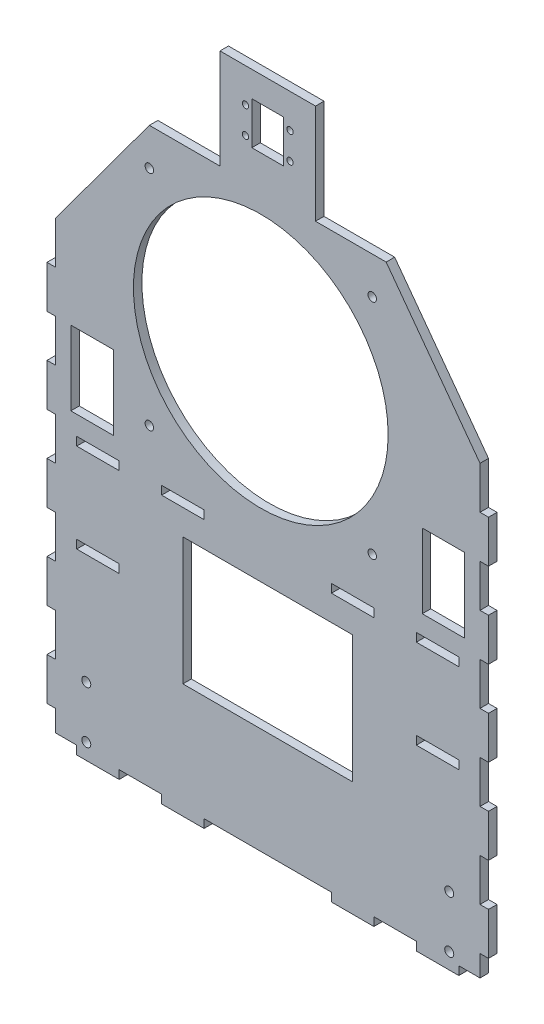
SolidWorks part; units mm, degrees
ref_plane "Přední rovina" through (0, 0, 0) normal (0, 0, 1) x (1, 0, 0)
ref_plane "Horní rovina" through (0, 0, 0) normal (0, 1, 0) x (1, 0, 0)
ref_plane "Pravá rovina" through (0, 0, 0) normal (1, 0, 0) x (0, 0, -1)
sketch "Skica1" plane through (0, 0, 0) normal (0, 0, 1) x (1, 0, 0)
  line L0 (-100, 0) -> (-100, -95.4761)
  line L1 (-200, 0) -> (0, 0)
  line L2 (-200, 0) -> (-200, 270)
  line L3 (-200, 270) -> (0, 270)
  line L4 (0, 0) -> (0, 270)
  line L5 (-190, 0) -> (-170, 0)
  line L6 (-190, 0) -> (-190, -4)
  line L7 (-190, -4) -> (-170, -4)
  line L8 (-170, 0) -> (-170, -4)
  line L9 (-150, 0) -> (-130, 0)
  line L10 (-150, 0) -> (-150, -4)
  line L11 (-150, -4) -> (-130, -4)
  line L12 (-130, 0) -> (-130, -4)
  line L13 (-110, 0) -> (-90, 0)
  line L14 (-110, 0) -> (-110, -4)
  line L15 (-110, -4) -> (-90, -4)
  line L16 (-90, 0) -> (-90, -4)
  line L17 (-50, -4) -> (-70, -4)
  line L18 (-70, 0) -> (-70, -4)
  line L19 (-50, 0) -> (-70, 0)
  line L20 (-50, 0) -> (-50, -4)
  line L21 (-10, -4) -> (-30, -4)
  line L22 (-30, 0) -> (-30, -4)
  line L23 (-10, 0) -> (-30, 0)
  line L24 (-10, 0) -> (-10, -4)
  line L25 (0, 150) -> (4, 150)
  line L26 (-200, 10) -> (-204, 10)
  line L27 (-200, 10) -> (-200, 30)
  line L28 (-200, 30) -> (-204, 30)
  line L29 (-204, 10) -> (-204, 30)
  line L30 (-200, 50) -> (-204, 50)
  line L31 (-200, 50) -> (-200, 70)
  line L32 (-200, 70) -> (-204, 70)
  line L33 (-204, 50) -> (-204, 70)
  line L34 (-200, 90) -> (-204, 90)
  line L35 (-200, 90) -> (-200, 110)
  line L36 (-200, 110) -> (-204, 110)
  line L37 (-204, 90) -> (-204, 110)
  line L38 (-200, 130) -> (-204, 130)
  line L39 (-200, 130) -> (-200, 150)
  line L40 (-200, 150) -> (-204, 150)
  line L41 (-204, 130) -> (-204, 150)
  line L42 (4, 130) -> (4, 150)
  line L43 (0, 130) -> (4, 130)
  line L44 (0, 130) -> (0, 150)
  line L45 (0, 110) -> (4, 110)
  line L46 (4, 90) -> (4, 110)
  line L47 (0, 90) -> (4, 90)
  line L48 (0, 90) -> (0, 110)
  line L49 (0, 70) -> (4, 70)
  line L50 (4, 50) -> (4, 70)
  line L51 (0, 50) -> (4, 50)
  line L52 (0, 50) -> (0, 70)
  line L53 (0, 30) -> (4, 30)
  line L54 (4, 10) -> (4, 30)
  line L55 (0, 10) -> (4, 10)
  line L56 (0, 10) -> (0, 30)
  line L57 (-155.7817, 270) -> (-200, 210)
  line L58 (-190, 126) -> (-170, 126)
  line L59 (-190, 126) -> (-190, 122)
  line L60 (-190, 122) -> (-170, 122)
  line L61 (-170, 126) -> (-170, 122)
  line L62 (-150, 126) -> (-130, 126)
  line L63 (-150, 126) -> (-150, 122)
  line L64 (-150, 122) -> (-130, 122)
  line L65 (-130, 126) -> (-130, 122)
  line L66 (-110, 126) -> (-90, 126)
  line L67 (-110, 126) -> (-110, 122)
  line L68 (-110, 122) -> (-90, 122)
  line L69 (-90, 126) -> (-90, 122)
  line L70 (-70, 126) -> (-50, 126)
  line L71 (-70, 126) -> (-70, 122)
  line L72 (-70, 122) -> (-50, 122)
  line L73 (-50, 126) -> (-50, 122)
  line L74 (-30, 126) -> (-10, 126)
  line L75 (-30, 126) -> (-30, 122)
  line L76 (-30, 122) -> (-10, 122)
  line L77 (-10, 126) -> (-10, 122)
  line L78 (-200, 170) -> (-204, 170)
  line L79 (-200, 170) -> (-200, 190)
  line L80 (-200, 190) -> (-204, 190)
  line L81 (-204, 170) -> (-204, 190)
  line L82 (-44.2183, 270) -> (0, 210)
  line L83 (0, 190) -> (4, 190)
  line L84 (4, 170) -> (4, 190)
  line L85 (0, 170) -> (4, 170)
  line L86 (0, 170) -> (0, 190)
  line L87 (-100, 56.76) -> (-100, -197.3379) construction
  line L88 (-122.5, 270) -> (-77.5, 270)
  line L89 (-122.5, 270) -> (-122.5, 317)
  line L90 (-122.5, 317) -> (-77.5, 317)
  line L91 (-77.5, 270) -> (-77.5, 317)
  line L92 (-107.5, 305) -> (-92.5, 305)
  line L93 (-107.5, 305) -> (-107.5, 285)
  line L94 (-107.5, 285) -> (-92.5, 285)
  line L95 (-92.5, 305) -> (-92.5, 285)
  line L96 (-140, 50) -> (-60, 50)
  line L97 (-140, 50) -> (-140, 110)
  line L98 (-140, 110) -> (-60, 110)
  line L99 (-60, 50) -> (-60, 110)
  line L100 (-172.7858, 135) -> (-192.7858, 135)
  line L101 (-172.7858, 135) -> (-172.7858, 170)
  line L102 (-172.7858, 170) -> (-192.7858, 170)
  line L103 (-192.7858, 135) -> (-192.7858, 170)
  line L104 (-27.2142, 170) -> (-7.2142, 170)
  line L105 (-27.2142, 135) -> (-27.2142, 170)
  line L106 (-27.2142, 135) -> (-7.2142, 135)
  line L107 (-7.2142, 135) -> (-7.2142, 170)
  line L108 (-190, 80) -> (-170, 84) construction
  line L109 (-10, 84) -> (-30, 84)
  line L110 (-10, 84) -> (-10, 80)
  line L111 (-10, 80) -> (-30, 80)
  line L112 (-30, 84) -> (-30, 80)
  line L113 (-10, 84) -> (-30, 80) construction
  line L114 (-10, 80) -> (-30, 84) construction
  line L115 (-190, 84) -> (-170, 80) construction
  line L116 (-170, 84) -> (-170, 80)
  line L117 (-190, 80) -> (-170, 80)
  line L118 (-190, 84) -> (-190, 80)
  line L119 (-190, 84) -> (-170, 84)
  line L120 (-14.5, 28) -> (-14.5, 3.5) construction
  circle A0 centre (-103.2817, 200) radius 60
  circle A1 centre (-155.7817, 252.5) radius 2
  circle A2 centre (-50.7817, 252.5) radius 2
  circle A3 centre (-50.7817, 147.5) radius 2
  circle A4 centre (-155.7817, 147.5) radius 2
  circle A5 centre (-110.5, 301) radius 1.5
  circle A6 centre (-89.5, 301) radius 1.5
  circle A7 centre (-89.5, 288.5) radius 1.5
  circle A8 centre (-110.5, 288.5) radius 1.5
  circle A9 centre (-14.5, 3.5) radius 2.125
  circle A10 centre (-14.5, 28) radius 2.125
  circle A11 centre (-185.5, 28) radius 2.125
  circle A12 centre (-185.5, 3.5) radius 2.125
  point P89 (-200, 210)
  point P93 (-155.7817, 270)
  point P128 (-20, 82)
  point P138 (-10, 82)
  point P140 (-50, 124)
  point P146 (-180, 82)
  point P149 (0, 0)
  dimension "D3" = 120
  dimension "D4" = 70
  dimension "D6" = 4
  dimension "D7" = 4
  dimension "D8" = 4
  dimension "D9" = 4
  dimension "D35" = 3
  dimension "D36" = 3
  dimension "D37" = 3
  dimension "D38" = 3
  dimension "D67" = 14.5
  dimension "D68" = 4.25
  dimension "D71" = 7.5
  dimension "D1" = 270
  dimension "D2" = 200
  dimension "D5" = 105
  dimension "D10" = 105
  dimension "D11" = 52.5
  dimension "D12" = 52.5
  dimension "D13" = 20
  dimension "D14" = 20
  dimension "D15" = 20
  dimension "D16" = 20
  dimension "D17" = 10
  dimension "D18" = 20
  dimension "D19" = 4
  dimension "D20" = 10
  dimension "D21" = 20
  dimension "D22" = 20
  dimension "D23" = 20
  dimension "D24" = 20
  dimension "D25" = 20
  dimension "D26" = 20
  dimension "D27" = 20
  dimension "D28" = 4
  dimension "D29" = 4
  dimension "D30" = 20
  dimension "D31" = 20
  dimension "D32" = 20
  dimension "D33" = 4
  dimension "D34" = 45
  dimension "D39" = 12.5
  dimension "D40" = 21
  dimension "D41" = 12
  dimension "D42" = 16
  dimension "D43" = 12
  dimension "D44" = 15
  dimension "D45" = 3
  dimension "D46" = 20
  dimension "D47" = 22.5
  dimension "D48" = 60
  dimension "D49" = 80
  dimension "D50" = 50
  dimension "D51" = 40
  dimension "D52" = 10
  dimension "D53" = 20
  dimension "D54" = 5
  dimension "D55" = 35
  dimension "D56" = 15
  dimension "D57" = 20
  dimension "D58" = 4
  dimension "D59" = 80
  dimension "D60" = 0
  dimension "D61" = 10
  dimension "D62" = 20
  dimension "D63" = 20
  dimension "D64" = 20
  dimension "D65" = 20
  dimension "D66" = 20
  dimension "D69" = 24.5
extrude "Přidat vysunutím1" add sketch "Skica1" along normal blind 4
